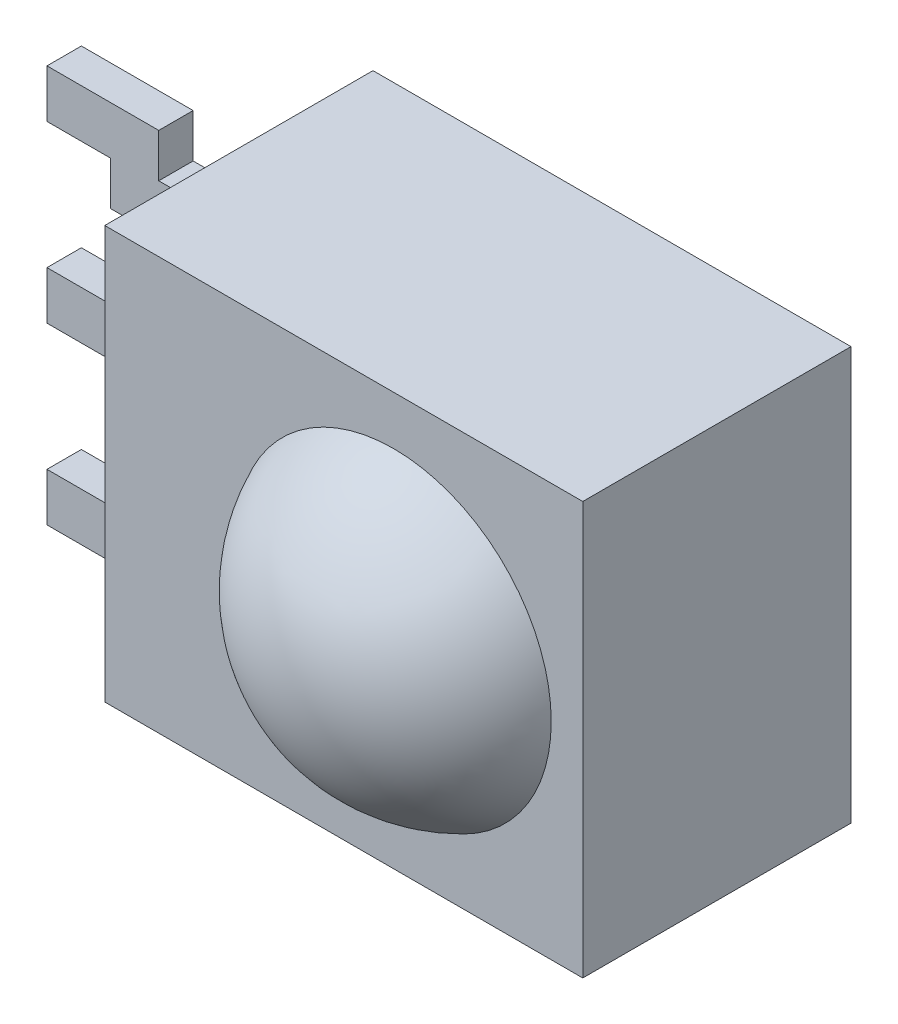
SolidWorks part; units mm, degrees
ref_plane "Front" through (0, 0, 0) normal (0, 0, 1) x (1, 0, 0)
ref_plane "Top" through (0, 0, 0) normal (0, 1, 0) x (1, 0, 0)
ref_plane "Right" through (0, 0, 0) normal (1, 0, 0) x (0, 0, -1)
sketch "Sketch1" plane through (0, 0, 0) normal (0, 0, 1) x (1, 0, 0)
  line L1 (-3.475, -3) -> (3.475, -3)
  line L2 (-3.475, -3) -> (-3.475, 3)
  line L3 (-3.475, 3) -> (3.475, 3)
  line L4 (3.475, -3) -> (3.475, 3)
  line L5 (-3.475, -3) -> (3.475, 3) construction
  line L6 (-3.475, 3) -> (3.475, -3) construction
  point P0 (0, 0)
  dimension "D1" = 6.95
  dimension "D2" = 6
extrude "Boss-Extrude1" add sketch "Sketch1" along normal mid plane 3.9
sketch "Sketch3" plane through (-3.475, 0, 0) normal (-1, 0, 0) x (0, 0, 1)
  line L1 (-0.25, 2.255) -> (0.25, 2.255)
  line L2 (-0.25, 2.255) -> (-0.25, 1.555)
  line L3 (-0.25, 1.555) -> (0.25, 1.555)
  line L4 (0.25, 2.255) -> (0.25, 1.555)
  line L5 (-0.25, 2.255) -> (0.25, 1.555) construction
  line L6 (-0.25, 1.555) -> (0.25, 2.255) construction
  line L7 (-0.25, 0.35) -> (0.25, 0.35)
  line L8 (-0.25, 0.35) -> (-0.25, -0.35)
  line L9 (-0.25, -0.35) -> (0.25, -0.35)
  line L10 (0.25, 0.35) -> (0.25, -0.35)
  line L11 (-0.25, 0.35) -> (0.25, -0.35) construction
  line L12 (-0.25, -0.35) -> (0.25, 0.35) construction
  line L13 (-0.25, -1.555) -> (0.25, -1.555)
  line L14 (-0.25, -1.555) -> (-0.25, -2.255)
  line L15 (-0.25, -2.255) -> (0.25, -2.255)
  line L16 (0.25, -1.555) -> (0.25, -2.255)
  line L17 (-0.25, -1.555) -> (0.25, -2.255) construction
  line L18 (-0.25, -2.255) -> (0.25, -1.555) construction
  point P0 (0, 1.905)
  point P5 (0, 0)
  point P11 (0, -1.905)
  dimension "D1" = 0.7
  dimension "D2" = 1.905
  dimension "D3" = 1.905
  dimension "D4" = 0.5
sketch "Sketch5" plane through (0, 0, 0) normal (0, 0, 1) x (1, 0, 0)
  line L0 (-3.475, 1.905) -> (-4.74, 1.905)
  line L1 (-4.74, 1.905) -> (-4.74, 2.54)
  line L2 (-4.74, 2.54) -> (-8.2375, 2.54)
  line L3 (3.475, -3) -> (3.475, 3) construction
  line L4 (-3.475, 3) -> (-3.475, -3) construction
  dimension "D1" = 8.215
  dimension "D2" = 2.54
  dimension "D3" = 4.7625
sketch "Sketch6" plane through (-3.475, 0, 0) normal (-1, 0, 0) x (0, 0, 1)
  line L1 (-0.25, 2.255) -> (0.25, 2.255)
  line L2 (-0.25, 2.255) -> (-0.25, 1.555)
  line L3 (-0.25, 1.555) -> (0.25, 1.555)
  line L4 (0.25, 2.255) -> (0.25, 1.555)
sweep "Sweep2" add profiles "Sketch6" path "Sketch5"
sketch "Sketch7" plane through (-3.475, 0, 0) normal (-1, 0, 0) x (0, 0, 1)
  line L1 (-0.25, 0.35) -> (0.25, 0.35)
  line L2 (-0.25, 0.35) -> (-0.25, -0.35)
  line L3 (-0.25, -0.35) -> (0.25, -0.35)
  line L4 (0.25, 0.35) -> (0.25, -0.35)
sketch "Sketch8" plane through (-3.475, 0, 0) normal (-1, 0, 0) x (0, 0, 1)
  line L1 (-0.25, -1.555) -> (0.25, -1.555)
  line L2 (-0.25, -1.555) -> (-0.25, -2.255)
  line L3 (-0.25, -2.255) -> (0.25, -2.255)
  line L4 (0.25, -1.555) -> (0.25, -2.255)
extrude "Boss-Extrude3" add sketch "Sketch7" along normal up to surface (4.7625 mm away) separate body up to face at (-8.2375, 2.54, 0)
sketch "Sketch10" plane through (0, 0, 0) normal (0, 0, 1) x (1, 0, 0)
  line L0 (-3.475, -1.905) -> (-4.74, -1.905)
  line L1 (-4.74, -1.905) -> (-4.74, -2.54)
  line L2 (-4.74, -2.54) -> (-8.2375, -2.54)
  line L3 (-8.2375, 2.19) -> (-8.2375, 2.89) construction
  line L4 (-3.475, 1.905) -> (-4.74, 1.905) construction
  line L5 (-4.74, 1.905) -> (-4.74, 2.54) construction
  line L6 (-4.74, 2.54) -> (-8.2375, 2.54) construction
  line L7 (3.475, -3) -> (3.475, 3) construction
  dimension "D1" = 8.215
  dimension "D2" = 2.54
sweep "Sweep3" add profiles "Sketch8" path "Sketch10"
sketch "Sketch4" plane through (0, 0, 0) normal (0, 1, 0) x (1, 0, 0)
  line L0 (-1.5663, -1.95) -> (0.725, -1.95)
  line L1 (3.475, -1.95) -> (-3.475, -1.95) construction
  line L2 (-4.775, 0.9385) -> (-4.775, -0.806) construction
  line L4 (0.725, -3.45) -> (0.725, -1.95) construction
  line L5 (3.475, -1.95) -> (3.475, 1.95) construction
  line L6 (0.725, -1.95) -> (0.725, -3.45)
  arc A0 (-1.5663, -1.95) -> (0.725, -3.45) centre (0.725, -0.95) ccw
  point P2 (0.725, -3.45)
  dimension "D2" = 2.5
  dimension "D1" = 1.5
  dimension "D3" = 2.75
revolve "Revolve6" add sketch "Sketch4" angle 360 about L6
sketch "Sketch11" plane through (0, 0, -0.25) normal (0, 0, -1) x (-1, 0, 0)
  line L0 (5.09, 2.19) -> (8.2375, 2.19) construction
  line L1 (8.2375, 2.89) -> (7.7375, 2.89)
  line L2 (8.2375, 2.89) -> (8.2375, 2.19)
  line L3 (8.2375, 2.19) -> (7.7375, 2.19)
  line L4 (7.7375, 2.89) -> (7.7375, 2.19)
  line L5 (8.2375, -0.35) -> (3.475, -0.35) construction
  line L6 (8.2375, 0.35) -> (7.7375, 0.35)
  line L7 (8.2375, 0.35) -> (8.2375, -0.35)
  line L8 (8.2375, -0.35) -> (7.7375, -0.35)
  line L9 (7.7375, 0.35) -> (7.7375, -0.35)
  line L10 (4.39, -2.89) -> (8.2375, -2.89) construction
  line L11 (8.2375, -2.19) -> (7.7375, -2.19)
  line L12 (8.2375, -2.19) -> (8.2375, -2.89)
  line L13 (8.2375, -2.89) -> (7.7375, -2.89)
  line L14 (7.7375, -2.19) -> (7.7375, -2.89)
  dimension "D1" = 0.5
extrude "Boss-Extrude4" add sketch "Sketch11" along normal blind 2.54
sketch "Sketch12" plane through (0, 0, 0.25) normal (0, 0, 1) x (1, 0, 0)
  line L0 (-6.015, 3.6678) -> (-6.015, -3.2512)
  line L1 (-3.475, 3) -> (-3.475, -3) construction
  dimension "D1" = 2.54
extrude "Cut-Extrude1" cut sketch "Sketch12" against normal through all and the other way through all flip side to cut
